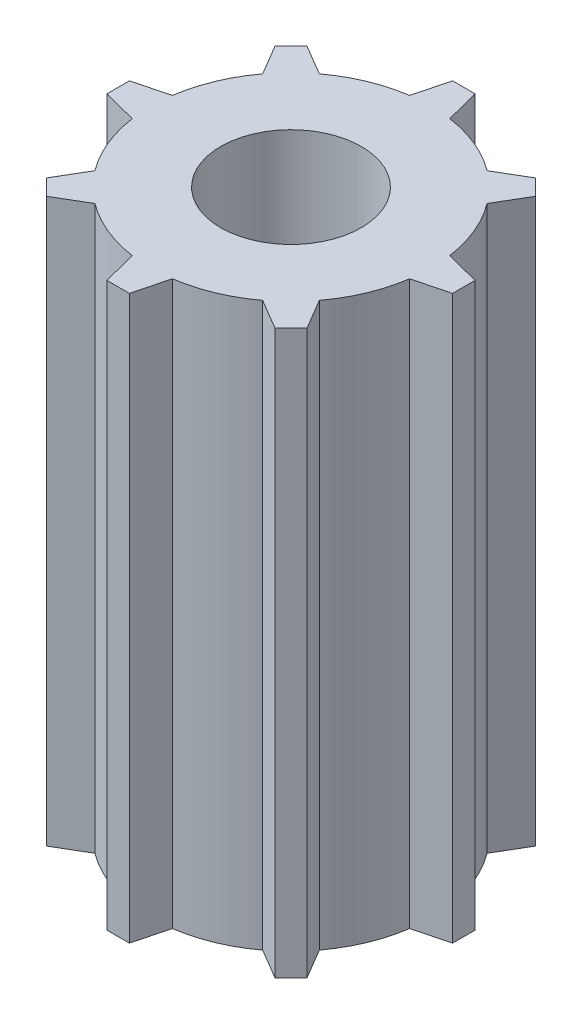
SolidWorks part; units mm, degrees
ref_plane "Front Plane" through (0, 0, 0) normal (0, 0, 1) x (1, 0, 0)
ref_plane "Top Plane" through (0, 0, 0) normal (0, 1, 0) x (1, 0, 0)
ref_plane "Right Plane" through (0, 0, 0) normal (1, 0, 0) x (0, 0, -1)
sketch "Sketch8" plane through (0, 0, 0) normal (0, 1, 0) x (1, 0, 0)
  line L1 (-0.9058, 6.2594) -> (-0.508, 7.8002)
  line L3 (0.9058, 6.2594) -> (0.508, 7.8002)
  line L4 (-0.508, 7.8002) -> (0.508, 7.8002)
  line L5 (5.0666, 3.7855) -> (5.8748, 5.1564)
  line L6 (3.7855, 5.0666) -> (5.1564, 5.8748)
  line L7 (5.1564, 5.8748) -> (5.8748, 5.1564)
  line L8 (6.2594, -0.9058) -> (7.8002, -0.508)
  line L9 (6.2594, 0.9058) -> (7.8002, 0.508)
  line L10 (7.8002, 0.508) -> (7.8002, -0.508)
  line L11 (3.7855, -5.0666) -> (5.1564, -5.8748)
  line L12 (5.0666, -3.7855) -> (5.8748, -5.1564)
  line L13 (5.8748, -5.1564) -> (5.1564, -5.8748)
  line L14 (-0.9058, -6.2594) -> (-0.508, -7.8002)
  line L15 (0.9058, -6.2594) -> (0.508, -7.8002)
  line L16 (0.508, -7.8002) -> (-0.508, -7.8002)
  line L17 (-5.0666, -3.7855) -> (-5.8748, -5.1564)
  line L18 (-3.7855, -5.0666) -> (-5.1564, -5.8748)
  line L19 (-5.1564, -5.8748) -> (-5.8748, -5.1564)
  line L20 (-6.2594, 0.9058) -> (-7.8002, 0.508)
  line L21 (-6.2594, -0.9058) -> (-7.8002, -0.508)
  line L22 (-7.8002, -0.508) -> (-7.8002, 0.508)
  line L23 (-3.7855, 5.0666) -> (-5.1564, 5.8748)
  line L24 (-5.0666, 3.7855) -> (-5.8748, 5.1564)
  line L25 (-5.8748, 5.1564) -> (-5.1564, 5.8748)
  arc A0 (-0.9058, 6.2594) -> (-3.7855, 5.0666) centre (0, 0) ccw
  arc A1 (-5.0666, 3.7855) -> (-6.2594, 0.9058) centre (0, 0) ccw
  arc A2 (-6.2594, -0.9058) -> (-5.0666, -3.7855) centre (0, 0) ccw
  arc A3 (-3.7855, -5.0666) -> (-0.9058, -6.2594) centre (0, 0) ccw
  arc A4 (0.9058, -6.2594) -> (3.7855, -5.0666) centre (0, 0) ccw
  arc A5 (5.0666, -3.7855) -> (6.2594, -0.9058) centre (0, 0) ccw
  arc A6 (6.2594, 0.9058) -> (5.0666, 3.7855) centre (0, 0) ccw
  arc A7 (3.7855, 5.0666) -> (0.9058, 6.2594) centre (0, 0) ccw
  point P6 (0, 6.3246)
  point P40 (0, 0)
  dimension "D1" = 12.6492
  dimension "D2" = 8
  dimension "D4" = 1.016
extrude "Boss-Extrude4" add sketch "Sketch8" along normal blind 25.4
sketch "Sketch9" plane through (0, 25.4, 0) normal (0, 1, 0) x (1, 0, 0)
  circle A0 centre (0, 0) radius 3.175
  dimension "D1" = 6.35
extrude "Cut-Extrude3" cut sketch "Sketch9" against normal blind 30.48
